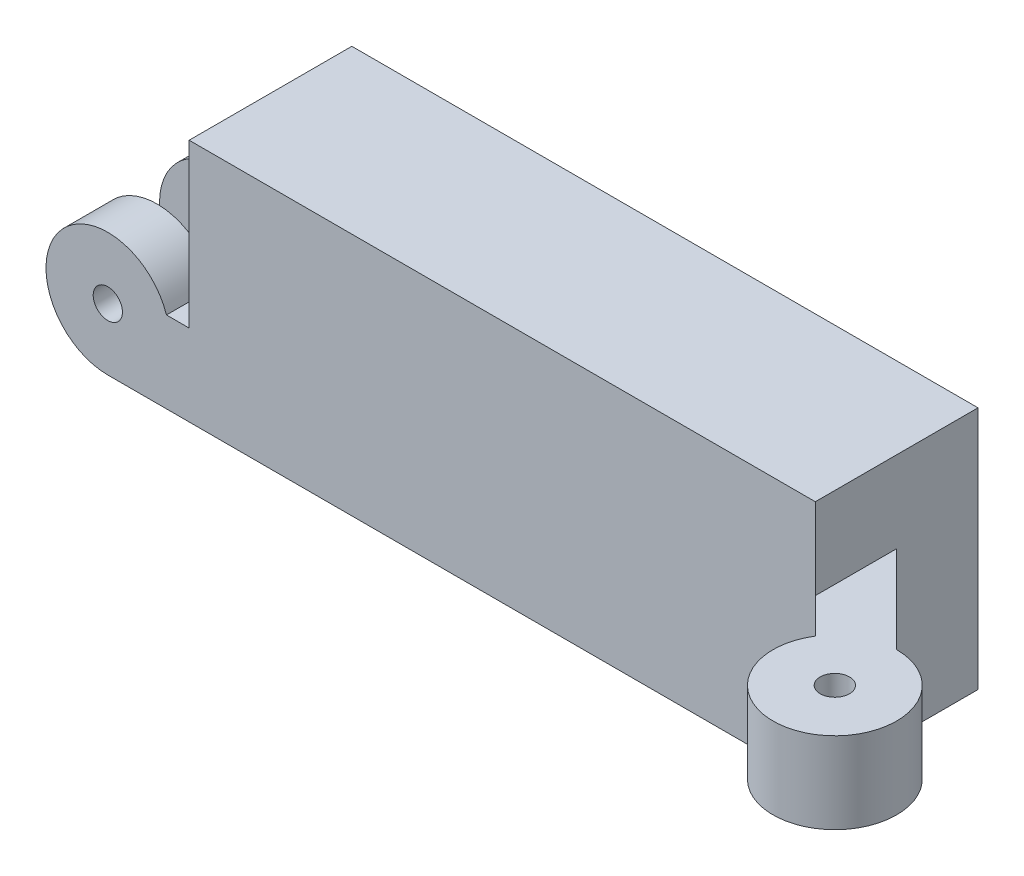
SolidWorks part; units mm, degrees
material "ABS"
ref_plane "Plan de face" through (0, 0, 0) normal (0, 0, 1) x (1, 0, 0)
ref_plane "Plan de dessus" through (0, 0, 0) normal (0, 1, 0) x (1, 0, 0)
ref_plane "Plan de droite" through (0, 0, 0) normal (1, 0, 0) x (0, 0, -1)
sketch "Sketch1" plane through (0, 0, 0) normal (0, 0, 1) x (1, 0, 0)
  line L0 (0, 0) -> (48.8813, 0)
  line L1 (48.8813, 0) -> (48.8813, 19.05)
  line L2 (48.8813, 19.05) -> (0, 19.05)
  line L3 (0, 19.05) -> (0, 0)
  dimension "D1" = 48.8813
  dimension "D2" = 19.05
extrude "Boss-Extrude2" add sketch "Sketch1" along normal blind 12.7
sketch "Sketch2" plane through (0, 0, 0) normal (0, 0, -1) x (-1, 0, 0)
  line L0 (0, 0) -> (6.35, 0)
  line L1 (6.35, 0) -> (6.35, 6.35)
  line L2 (6.35, 6.35) -> (0, 6.35)
  line L3 (0, 19.05) -> (0, 0) construction
  line L4 (0, 6.35) -> (0, 0)
  circle A0 centre (6.35, 4.826) radius 4.826
  circle A1 centre (6.35, 4.826) radius 1.143
  line M6 (0, 0) -> (0, 19.05)
  dimension "D3" = 9.652
  dimension "D4" = 2.286
  dimension "D1" = 6.35
  dimension "D2" = 6.35
extrude "Boss-Extrude3" add sketch "Sketch2" against normal blind 3.8365 contours A1 L1 A0 L2 | A1 L1 L2 A0 | A0 L2 L0 M6
pattern_linear "LPattern1" count 2 spacing 8.8635 along (0, 0, 1) of "Boss-Extrude3"
ref_plane "Plane1" through (0, 9.525, 0) normal (0, -1, 0) x (-1, 0, 0)
sketch "Sketch3" plane through (0, 0, 0) normal (0, -1, 0) x (1, 0, 0)
  line L0 (48.8813, 12.7) -> (48.8813, 6.35)
  line L1 (48.8813, 12.7) -> (55.7063, 19.525)
  line L2 (48.8813, 6.35) -> (55.7063, 13.175)
  line L3 (55.7063, 19.525) -> (55.7063, 13.175)
  line L4 (48.8813, 12.7) -> (48.8813, 0) construction
  circle A0 centre (55.7063, 18.001) radius 4.826
  circle A1 centre (55.7063, 18.001) radius 1.143
  line M3 (48.8813, 0) -> (48.8813, 12.7)
  dimension "D4" = 9.652
  dimension "D5" = 2.286
  dimension "D1" = 6.35
  dimension "D2" = 45
  dimension "D3" = 9.652
extrude "Boss-Extrude5" add sketch "Sketch3" along normal mid plane 6.35 from surface at -9.525 contours A1 L3 L1 | A1 L3 A0 L1 | A1 L1 A0 L3 | A0 L1 L2 M3
sketch "Sketch4" plane through (0, 0, 0) normal (0, 0, -1) x (-1, 0, 0)
  line L0 (-48.8813, 0) -> (-48.8813, 19.05) construction
  circle A0 centre (-45.5793, 9.525) radius 0.508
  circle A1 centre (-3.0673, 9.525) radius 0.508
  point P6 (0, 0)
  dimension "D3" = 1.016
  dimension "D4" = 1.016
  dimension "D1" = 42.512
  dimension "D2" = 3.302
extrude "Cut-Extrude1" cut sketch "Sketch4" against normal blind 7.62
